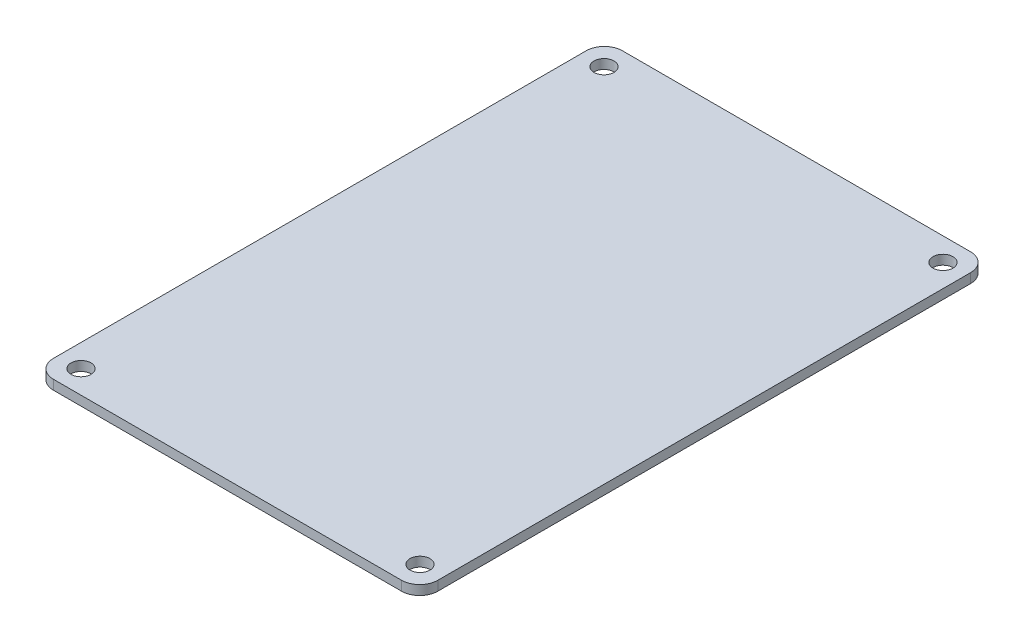
SolidWorks part; units mm, degrees
ref_plane "Front Plane" through (0, 0, 0) normal (0, 0, 1) x (1, 0, 0)
ref_plane "Top Plane" through (0, 0, 0) normal (0, 1, 0) x (1, 0, 0)
ref_plane "Right Plane" through (0, 0, 0) normal (1, 0, 0) x (0, 0, -1)
sketch "Sketch1" plane through (0, 0, 0) normal (0, 1, 0) x (1, 0, 0)
  line L0 (0, 47) -> (0, -47) construction
  line L1 (-31.75, 47) -> (31.75, 47)
  line L2 (-31.75, 47) -> (-31.75, -47)
  line L3 (-31.75, -47) -> (31.75, -47)
  line L4 (31.75, 47) -> (31.75, -47)
  line L5 (-31.75, 47) -> (31.75, -47) construction
  line L6 (-31.75, -47) -> (31.75, 47) construction
  line L7 (-31.75, 0) -> (31.75, 0) construction
  circle A0 centre (-28, 43.2) radius 1.65
  circle A1 centre (28, 43.2) radius 1.65
  circle A2 centre (28, -43.2) radius 1.65
  circle A3 centre (-28, -43.2) radius 1.65
  point P0 (0, 0)
  dimension "D3" = 3.3
  dimension "D1" = 63.5
  dimension "D2" = 94
  dimension "D4" = 56
  dimension "D5" = 86.4
extrude "Boss-Extrude1" add sketch "Sketch1" along normal blind 1.57
fillet "Fillet1" radius 3 4 edges at (-31.75, 0.785, -47) (31.75, 0.785, -47) (31.75, 0.785, 47) (-31.75, 0.785, 47)
